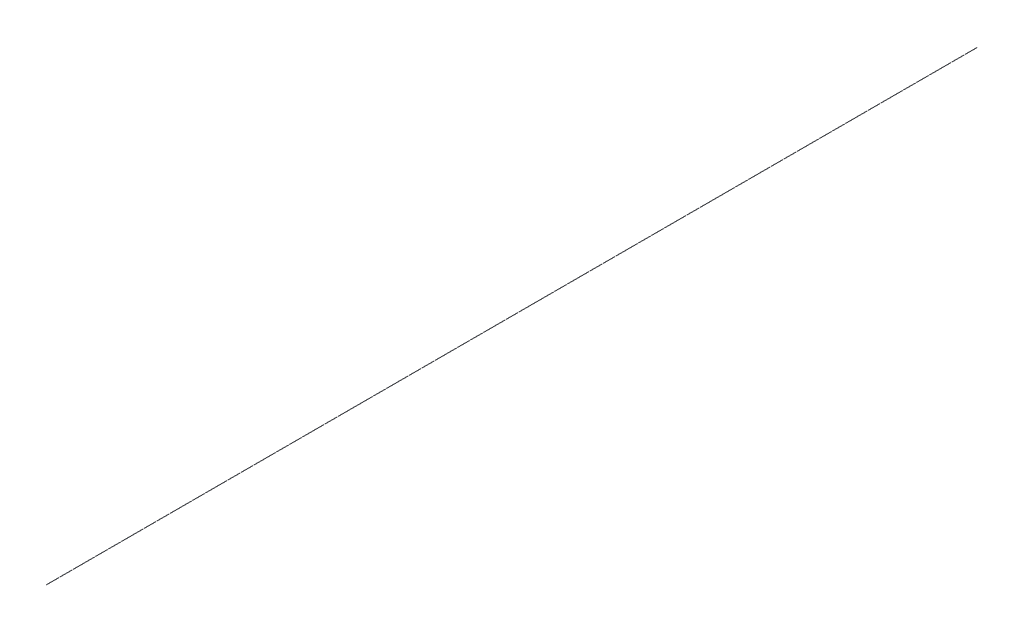
SolidWorks part; units mm, degrees
ref_plane "Front Plane" through (0, 0, 0) normal (0, 0, 1) x (1, 0, 0)
ref_plane "Top Plane" through (0, 0, 0) normal (0, 1, 0) x (1, 0, 0)
ref_plane "Right Plane" through (0, 0, 0) normal (1, 0, 0) x (0, 0, -1)
sketch "Sketch1" plane through (0, 0, 0) normal (0, 0, 1) x (1, 0, 0)
  circle A0 centre (0, 0) radius 5
  dimension "D1" = 10
extrude "Boss-Extrude1" add sketch "Sketch1" along normal blind 55000
